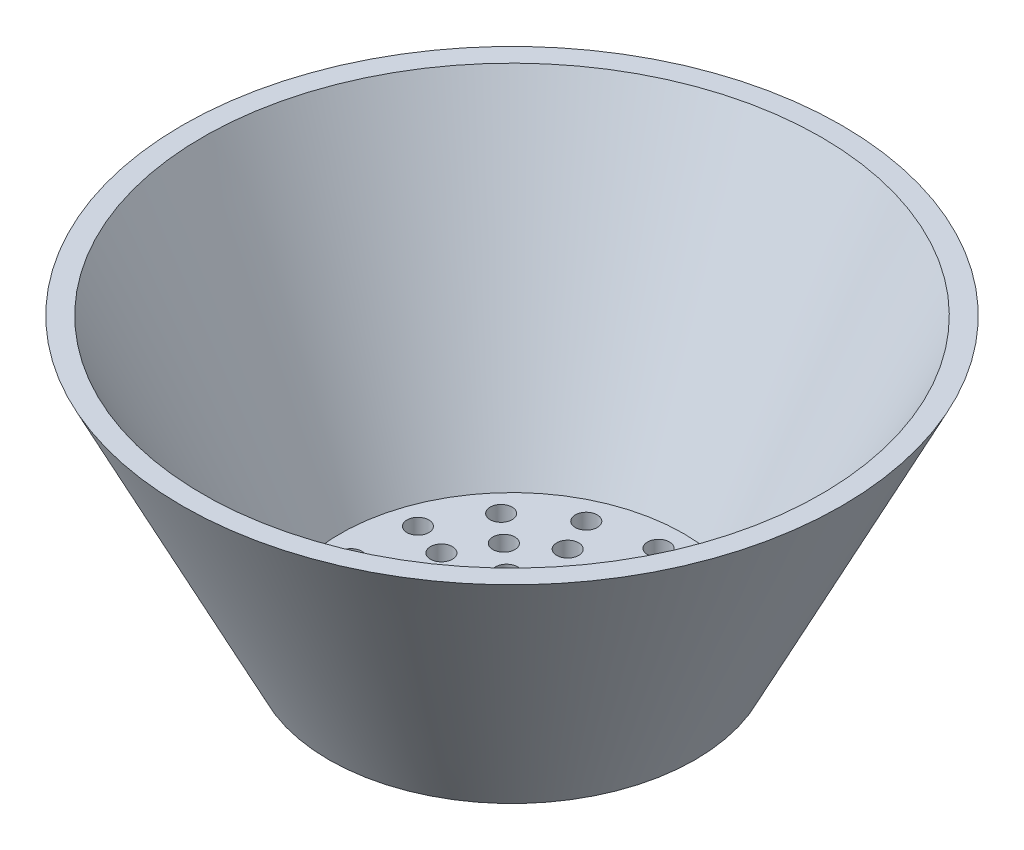
SolidWorks part; units mm, degrees
ref_plane "Front Plane" through (0, 0, 0) normal (0, 0, 1) x (1, 0, 0)
ref_plane "Top Plane" through (0, 0, 0) normal (0, 1, 0) x (1, 0, 0)
ref_plane "Right Plane" through (0, 0, 0) normal (1, 0, 0) x (0, 0, -1)
sketch "Sketch1" plane through (0, 0, 0) normal (0, 0, 1) x (1, 0, 0)
  line L0 (0, 0) -> (0, 80)
  line L2 (90, 80) -> (50, 0)
  line L3 (50, 0) -> (0, 0)
  line L6 (81.9098, 75) -> (46.9098, 5)
  line L7 (46.9098, 5) -> (5, 5)
  line L8 (5, 75) -> (81.9098, 75) construction
  line L9 (81.9098, 75) -> (84.4098, 80)
  line L10 (84.4098, 80) -> (90, 80)
  line L11 (0, 80) -> (90, 80) construction
  line L12 (5, 5) -> (0, 5)
  line L13 (5, 5) -> (5, 75) construction
  line L14 (0, 5) -> (0, 0)
  dimension "D1" = 90
  dimension "D2" = 50
  dimension "D3" = 80
  dimension "D4" = 5
revolve "Revolve1" add sketch "Sketch1" angle 360 about L0
sketch "Sketch3" plane through (0, 5, 0) normal (0, 1, 0) x (1, 0, 0)
  circle A0 centre (0, 40) radius 3
extrude "Cut-Extrude5" cut sketch "Sketch3" against normal blind 10
pattern_circular "CirPattern2" count 15 over 360 about axis through (0, 0, 0) along (0, 1, 0) of "Cut-Extrude5"
sketch "Sketch4" plane through (0, 5, 0) normal (0, 1, 0) x (1, 0, 0)
  circle A0 centre (0, 30) radius 3
  circle A1 centre (0, 20) radius 3
  circle A2 centre (0, 0) radius 2
  circle A3 centre (0, 10) radius 2
  dimension "D3" = 10
  dimension "D2" = 10
extrude "Cut-Extrude7" cut sketch "Sketch4" against normal blind 10
pattern_circular "CirPattern3" count 15 over 360 about axis through (0, 0, 0) along (0, 1, 0) of "Cut-Extrude7"
